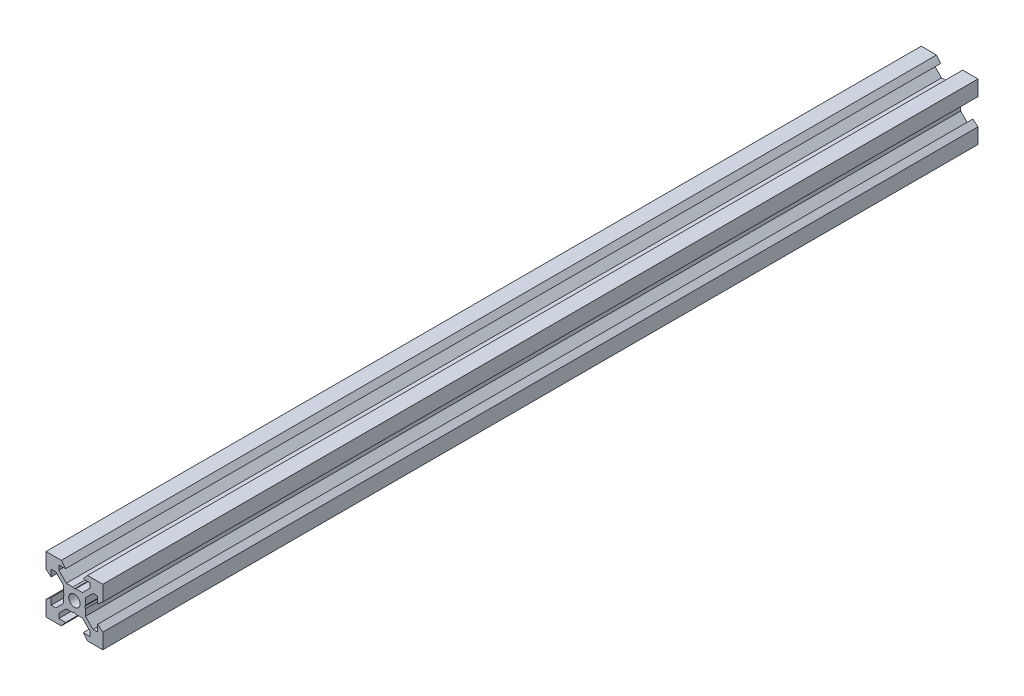
SolidWorks part; units mm, degrees
ref_plane "Front Plane" through (0, 0, 0) normal (0, 0, 1) x (1, 0, 0)
ref_plane "Top Plane" through (0, 0, 0) normal (0, 1, 0) x (1, 0, 0)
ref_plane "Right Plane" through (0, 0, 0) normal (1, 0, 0) x (0, 0, -1)
sketch "Sketch1" plane through (0, 0, 0) normal (0, 0, 1) x (1, 0, 0)
  line L0 (10, 10) -> (4.6104, 10) construction
  line L1 (10, 10) -> (10, 4.6104) construction
  line L2 (10, -10) -> (10, -4.6104) construction
  line L3 (10, -10) -> (4.6104, -10) construction
  line L4 (10, 10) -> (10, 4.6104)
  line L5 (6.5607, 5.5) -> (8.2, 5.5)
  line L6 (5.5, 8.2) -> (5.5, 6.5607)
  line L7 (10, 10) -> (4.6104, 10)
  line L8 (10, 10) -> (10, 4.6104)
  line L9 (6.5607, 5.5) -> (3.9, 2.8393)
  line L10 (5.5, 6.5607) -> (2.8393, 3.9)
  line L11 (10, 4.6104) -> (8.2, 3.1)
  line L12 (4.6104, 10) -> (3.1, 8.2)
  line L13 (8.2, 3.1) -> (8.2, 5.5)
  line L14 (3.1, 8.2) -> (5.5, 8.2)
  line L15 (-6.5607, 5.5) -> (-8.2, 5.5)
  line L16 (6.5607, -5.5) -> (8.2, -5.5)
  line L17 (3.1, -8.2) -> (5.5, -8.2)
  line L18 (8.2, -3.1) -> (8.2, -5.5)
  line L19 (4.6104, -10) -> (3.1, -8.2)
  line L20 (10, -4.6104) -> (8.2, -3.1)
  line L21 (0.5196, -3.9) -> (0, -3.6)
  line L22 (0.5196, 3.9) -> (0, 3.6)
  line L23 (3.6, 0) -> (3.9, -0.5196)
  line L24 (3.9, 0.5196) -> (3.6, 0)
  line L25 (3.9, 0.5196) -> (3.9, 2.8393)
  line L26 (2.8393, 3.9) -> (0.5196, 3.9)
  line L27 (3.9, -2.8393) -> (3.9, -0.5196)
  line L28 (2.8393, -3.9) -> (0.5196, -3.9)
  line L29 (5.5, -6.5607) -> (2.8393, -3.9)
  line L30 (6.5607, -5.5) -> (3.9, -2.8393)
  line L31 (10, -10) -> (10, -4.6104)
  line L32 (10, -10) -> (4.6104, -10)
  line L33 (5.5, -8.2) -> (5.5, -6.5607)
  line L34 (-6.5607, -5.5) -> (-8.2, -5.5)
  line L35 (10, -10) -> (10, -4.6104)
  line L36 (0, 0) -> (0, 8.2) construction
  line L37 (-10, -10) -> (-4.6104, -10) construction
  line L38 (-10, -10) -> (-10, -4.6104) construction
  line L39 (-10, 10) -> (-10, 4.6104) construction
  line L40 (-10, 10) -> (-4.6104, 10) construction
  line L41 (-10, -10) -> (-10, -4.6104)
  line L43 (-5.5, -8.2) -> (-5.5, -6.5607)
  line L44 (-10, -10) -> (-4.6104, -10)
  line L45 (-10, -10) -> (-10, -4.6104)
  line L46 (-6.5607, -5.5) -> (-3.9, -2.8393)
  line L47 (-5.5, -6.5607) -> (-2.8393, -3.9)
  line L48 (-2.8393, -3.9) -> (-0.5196, -3.9)
  line L49 (-3.9, -2.8393) -> (-3.9, -0.5196)
  line L50 (-2.8393, 3.9) -> (-0.5196, 3.9)
  line L51 (-3.9, 0.5196) -> (-3.9, 2.8393)
  line L52 (-3.9, 0.5196) -> (-3.6, 0)
  line L53 (-3.6, 0) -> (-3.9, -0.5196)
  line L54 (-0.5196, 3.9) -> (0, 3.6)
  line L55 (-0.5196, -3.9) -> (0, -3.6)
  line L56 (-10, -4.6104) -> (-8.2, -3.1)
  line L57 (-4.6104, -10) -> (-3.1, -8.2)
  line L58 (-8.2, -3.1) -> (-8.2, -5.5)
  line L59 (-3.1, -8.2) -> (-5.5, -8.2)
  line L60 (-10, -10) -> (10, -10) construction
  line L61 (-10, -10) -> (-10, 10) construction
  line L62 (-3.1, 8.2) -> (-5.5, 8.2)
  line L63 (-8.2, 3.1) -> (-8.2, 5.5)
  line L64 (-4.6104, 10) -> (-3.1, 8.2)
  line L65 (-10, 4.6104) -> (-8.2, 3.1)
  line L66 (-5.5, 6.5607) -> (-2.8393, 3.9)
  line L67 (-6.5607, 5.5) -> (-3.9, 2.8393)
  line L68 (-10, 10) -> (-10, 4.6104)
  line L69 (-10, 10) -> (-4.6104, 10)
  line L70 (-5.5, 8.2) -> (-5.5, 6.5607)
  line L71 (-10, 10) -> (10, 10) construction
  line L72 (-10, 10) -> (-10, 4.6104)
  line L73 (10, -10) -> (10, 10) construction
  line L74 (-10, -10) -> (10, 10) construction
  line L75 (-10, 10) -> (10, -10) construction
  circle A0 centre (0, 0) radius 2
  dimension "D7" = 4
  dimension "D1" = 20
  dimension "D2" = 5.3896
  dimension "D3" = 4.5
  dimension "D4" = 50
  dimension "D5" = 1.8
  dimension "D6" = 1.5104
  dimension "D8" = 5.5
  dimension "D9" = 120
  dimension "D10" = 0.3
  dimension "D11" = 2.3197
  dimension "D12" = 7.8
  dimension "D13" = 7.8
  dimension "D14" = 1.5
  dimension "D15" = 2.6607
extrude "Boss-Extrude1" add sketch "Sketch1" along normal mid plane 308.33 contours L70 L62 L64 L69 L68 L65 L63 L15 L67 L51 L52 L53 L49 L46 L34 L58 L56 L41 L44 L57 L59 L43 L47 L48 L55 L21 L28 L29 L33 L17 L19 L32 L31 L20 L18 L16 L30 L27 L23 L24 L25 L9 L5 L13 L11 L4 L7 L12 L14 L6 L10
